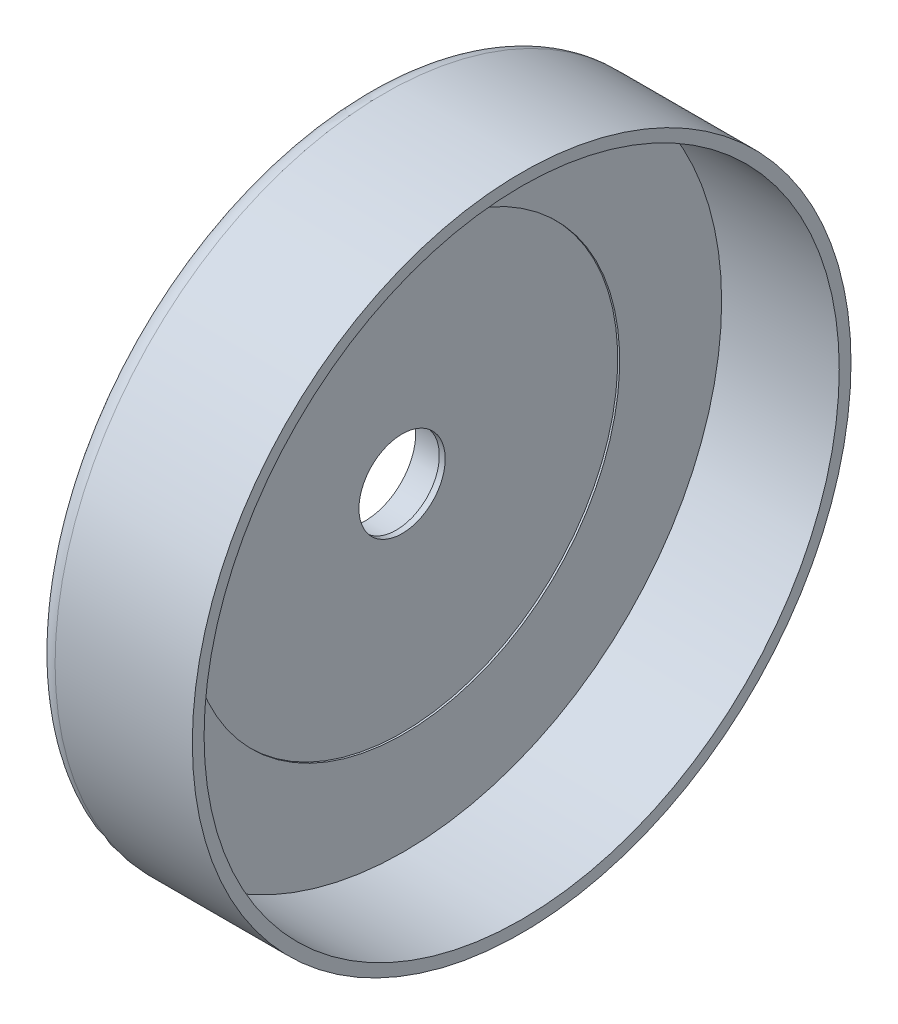
SolidWorks part; units mm, degrees
material "AISI 1020"
ref_plane "Front Plane" through (0, 0, 0) normal (0, 0, 1) x (1, 0, 0)
ref_plane "Top Plane" through (0, 0, 0) normal (0, 1, 0) x (1, 0, 0)
ref_plane "Right Plane" through (0, 0, 0) normal (1, 0, 0) x (0, 0, -1)
sketch "Sketch1" plane through (0, 0, 0) normal (0, 0, 1) x (1, 0, 0)
  line L0 (0, 0) -> (0, 81)
  line L1 (0, 81) -> (30, 81)
  line L2 (30, 81) -> (30, 84)
  line L3 (30, 84) -> (-10, 84)
  line L4 (-10, 84) -> (-10, 0)
  line L5 (-10, 0) -> (0, 0)
  line L6 (0, 0) -> (-2, 0) construction
  dimension "D1" = 81
  dimension "D2" = 30
  dimension "D3" = 10
  dimension "D4" = 3
revolve "Revolve1" add sketch "Sketch1" angle 360 about L5
fillet "Fillet1" radius 5 1 edges at (-10, 0, 84)
sketch "Sketch3" plane through (-10, 0, 0) normal (-1, 0, 0) x (0, 0, 1)
  circle A0 centre (0, 0) radius 11
  dimension "D1" = 22
extrude "Cut-Extrude2" cut sketch "Sketch3" against normal through all
sketch "Sketch4" plane through (69.6895, -35.7639, 15.6766) normal (0, 0, 1) x (1, 0, 0)
sketch "Sketch6" plane through (0, 0, 0) normal (0, 0, 1) x (1, 0, 0)
  line L0 (0, 0) -> (-0.5, 0)
  line L1 (-10, 0) -> (0, 0) construction
  line L2 (0, 0) -> (0, 55)
  line L3 (0, 0) -> (0, 81) construction
  line L4 (-0.5, 0) -> (-0.5, 55)
  line L5 (-0.5, 55) -> (0, 55)
revolve "Cut-Revolve2" cut sketch "Sketch6" angle 360 about L5
sketch "Sketch7" plane through (0, 0, 0) normal (0, 0, 1) x (1, 0, 0)
  line L0 (0, 0) -> (0, 13) construction
  line L1 (0, 0) -> (0, 81) construction
  line L3 (-0.5, 13) -> (-2, 12.9976)
  line L4 (-2, 11) -> (-2, 12.9976)
  line L5 (-0.5, 0) -> (-0.5, 55) construction
  line L6 (-2, 11) -> (-0.5, 11)
  line L7 (-0.5, 11) -> (-0.5, 13)
ref_plane "Plane1" through (-10, 0, 0) normal (-1, 0, 0) x (0, 0, 1)
sketch "Sketch9" plane through (-10, 0, 0) normal (-1, 0, 0) x (0, 0, 1)
  circle A0 centre (0, 0) radius 13
extrude "Cut-Extrude3" cut sketch "Sketch9" against normal blind 8
